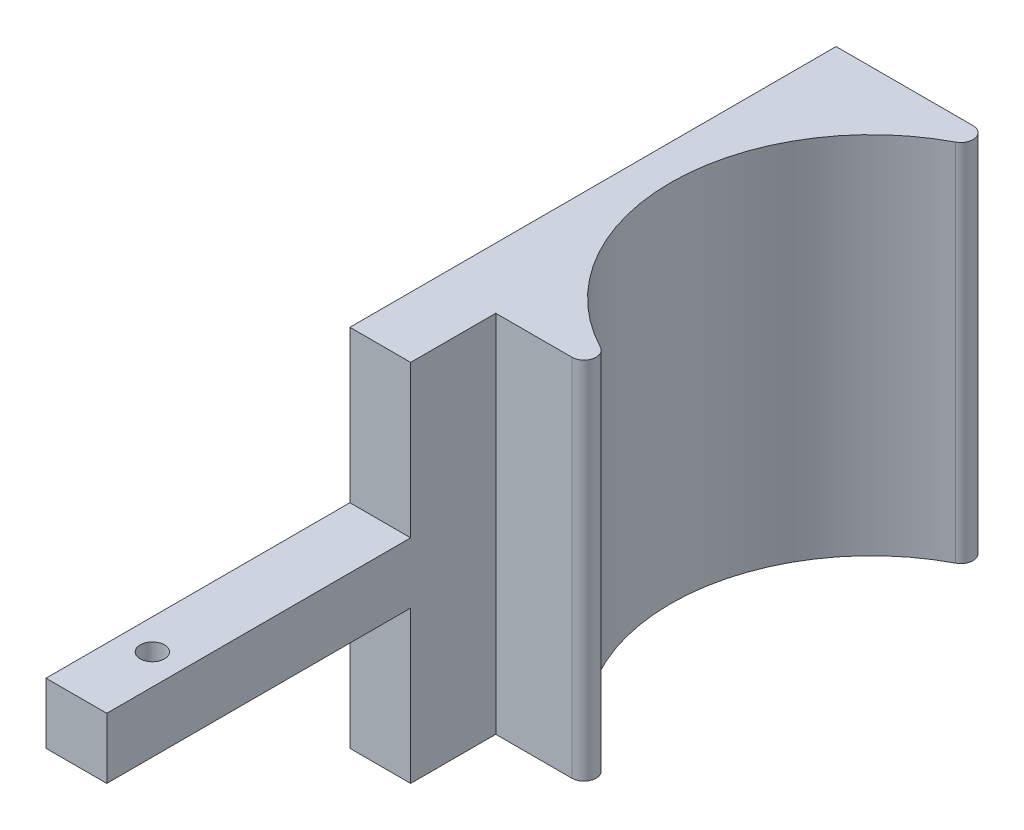
SolidWorks part; units mm, degrees
ref_plane "Front Plane" through (0, 0, 0) normal (0, 0, 1) x (1, 0, 0)
ref_plane "Top Plane" through (0, 0, 0) normal (0, 1, 0) x (1, 0, 0)
ref_plane "Right Plane" through (0, 0, 0) normal (1, 0, 0) x (0, 0, -1)
sketch "Sketch1" plane through (0, 0, 0) normal (0, 1, 0) x (1, 0, 0)
  line L0 (-4.2718, 52.0253) -> (24.4989, 52.0253)
  line L1 (-14.2718, 52.0253) -> (-4.2718, 52.0253)
  line L2 (-14.2718, 52.0253) -> (-14.2718, -77.9747)
  line L3 (-14.2718, -77.9747) -> (-4.2718, -77.9747)
  line L4 (-4.2718, -13.9747) -> (-4.2718, -77.9747)
  line L5 (-4.2718, -13.9747) -> (24.4989, -13.9747)
  arc A0 (24.4989, 52.0253) -> (24.4989, -13.9747) centre (24.4989, 19.0253) ccw
  dimension "D3" = 66
  dimension "D4" = 33
  dimension "D1" = 130
  dimension "D2" = 10
  dimension "D5" = 33
extrude "Boss-Extrude1" add sketch "Sketch1" along normal blind 60
sketch "Sketch2" plane through (0, 60, 0) normal (0, 1, 0) x (1, 0, 0)
  line L0 (-4.2718, -77.9747) -> (-4.2718, -13.9747) construction
  line L1 (-14.2718, -77.9747) -> (-4.2718, -77.9747)
  line L2 (-14.2718, -77.9747) -> (-14.2718, -27.9747)
  line L3 (-14.2718, -27.9747) -> (-4.2718, -27.9747)
  line L4 (-4.2718, -77.9747) -> (-4.2718, -27.9747)
  dimension "D1" = 50
extrude "Cut-Extrude1" cut sketch "Sketch2" against normal blind 25
sketch "Sketch3" plane through (0, 0, 0) normal (0, -1, 0) x (1, 0, 0)
  line L0 (-4.2718, 77.9747) -> (-4.2718, 13.9747) construction
  line L1 (-14.2718, 77.9747) -> (-4.2718, 77.9747)
  line L2 (-14.2718, 77.9747) -> (-14.2718, 27.9747)
  line L3 (-14.2718, 27.9747) -> (-4.2718, 27.9747)
  line L4 (-4.2718, 77.9747) -> (-4.2718, 27.9747)
  dimension "D1" = 50
extrude "Cut-Extrude2" cut sketch "Sketch3" against normal blind 25
fillet "Fillet1" radius 2 2 edges at (24.4989, 30, 13.9747) (24.4989, 30, -52.0253)
sketch "Sketch4" plane through (0, 35, 0) normal (0, 1, 0) x (1, 0, 0)
  line L0 (-14.2718, -77.9747) -> (-4.2718, -77.9747) construction
  circle A0 centre (-9.2718, -65.4747) radius 2
  dimension "D1" = 12.5
  dimension "D2" = 4
extrude "Cut-Extrude3" cut sketch "Sketch4" against normal blind 25 contours A0
